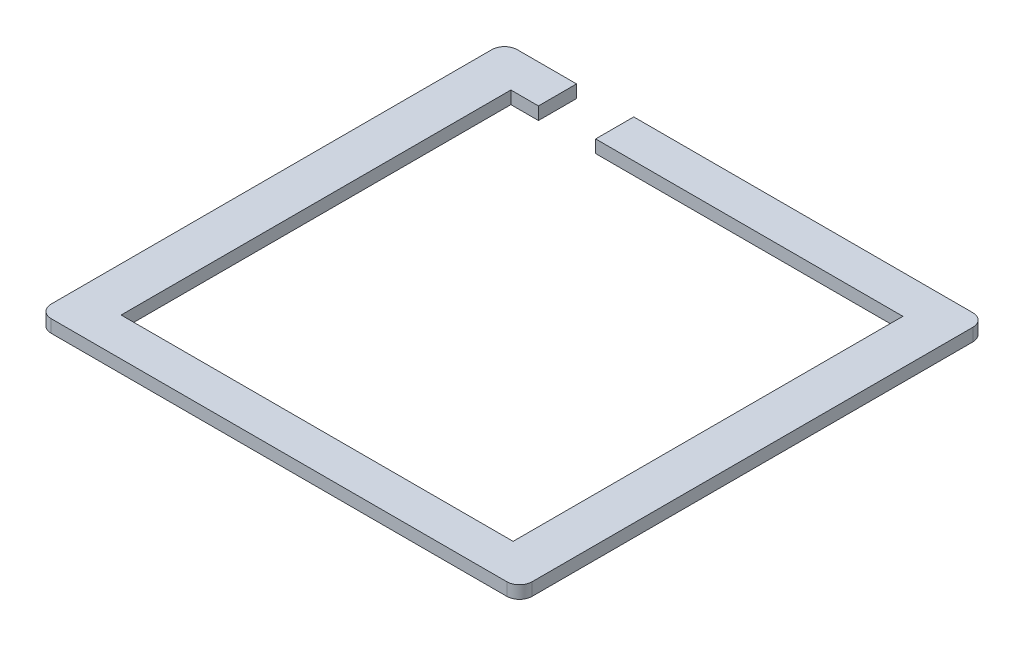
SolidWorks part; units mm, degrees
material "有机玻璃 (TM) GS 丙烯酸铸钣"
ref_plane "前视基准面" through (0, 0, 0) normal (0, 0, 1) x (1, 0, 0)
ref_plane "上视基准面" through (0, 0, 0) normal (0, 1, 0) x (1, 0, 0)
ref_plane "右视基准面" through (0, 0, 0) normal (1, 0, 0) x (0, 0, -1)
sketch "草图1" plane through (-129.6412, -2421.7881, -243.9405) normal (0, 1, 0) x (1, 0, 0)
  line L1 (-111.2311, -160.9249) -> (-49.5289, -160.9249)
  line L2 (-111.2311, -160.9249) -> (-111.2311, -222.2721)
  line L3 (-111.2311, -222.2721) -> (-49.5289, -222.2721)
  line L4 (-49.5289, -160.9249) -> (-49.5289, -222.2721)
  line L11 (-43.5289, -153.9249) -> (-97.892, -153.9249) construction
  line L12 (-116.2311, -154.9249) -> (-44.5289, -154.9249)
  line L13 (-118.2311, -156.9249) -> (-118.2311, -226.2721)
  line L14 (-116.2311, -228.2721) -> (-44.5289, -228.2721)
  line L15 (-42.5289, -156.9249) -> (-42.5289, -226.2721)
  line L16 (-41.5289, -227.2721) -> (-41.5289, -155.9249) construction
  line L17 (-119.2311, -155.9249) -> (-119.2311, -227.2721) construction
  line L18 (-117.2311, -229.2721) -> (-43.5289, -229.2721) construction
  arc A0 (-44.5289, -154.9249) -> (-42.5289, -156.9249) centre (-44.5289, -156.9249) cw
  arc A1 (-42.5289, -226.2721) -> (-44.5289, -228.2721) centre (-44.5289, -226.2721) cw
  arc A2 (-116.2311, -228.2721) -> (-118.2311, -226.2721) centre (-116.2311, -226.2721) cw
  arc A3 (-118.2311, -156.9249) -> (-116.2311, -154.9249) centre (-116.2311, -156.9249) cw
  dimension "D5" = 2
  dimension "D1" = 1
  dimension "D2" = 1
  dimension "D3" = 1
  dimension "D4" = 1
extrude "凸台-拉伸1" add sketch "草图1" along normal blind 2
sketch "草图2" plane through (0, -2419.7881, 0) normal (0, 1, 0) x (1, 0, 0)
  line L0 (-236.5332, 90.0156) -> (-236.5332, 83.0156) construction
  line L1 (-236.5332, 89.0156) -> (-227.5332, 89.0156)
  line L2 (-236.5332, 89.0156) -> (-236.5332, 83.0156)
  line L3 (-236.5332, 83.0156) -> (-227.5332, 83.0156)
  line L4 (-227.5332, 89.0156) -> (-227.5332, 83.0156)
  line L5 (-174.1701, 89.0156) -> (-245.8722, 89.0156) construction
  line L6 (-179.1701, 83.0156) -> (-240.8722, 83.0156) construction
  line L7 (-227.5332, 83.0156) -> (-227.5332, 90.0156) construction
extrude "切除-拉伸1" cut sketch "草图2" against normal blind 2
